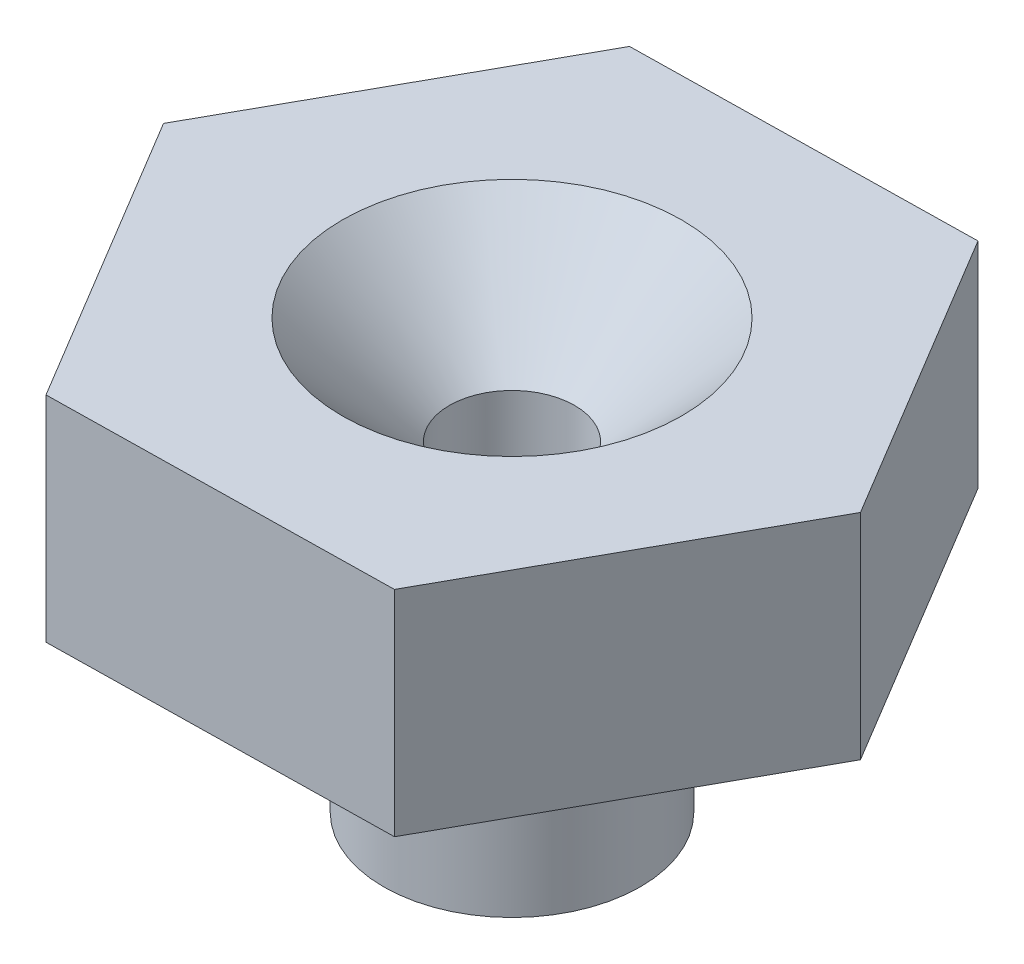
SolidWorks part; units mm, degrees
ref_plane "Front Plane" through (0, 0, 0) normal (0, 0, 1) x (1, 0, 0)
ref_plane "Top Plane" through (0, 0, 0) normal (0, 1, 0) x (1, 0, 0)
ref_plane "Right Plane" through (0, 0, 0) normal (1, 0, 0) x (0, 0, -1)
sketch "Sketch1" plane through (0, 0, 0) normal (0, 1, 0) x (1, 0, 0)
  line L1 (-15.9977, -0.2701) -> (-7.7649, -13.9895)
  line L2 (-7.7649, -13.9895) -> (8.2328, -13.7194)
  line L3 (8.2328, -13.7194) -> (15.9977, 0.2701)
  line L4 (15.9977, 0.2701) -> (7.7649, 13.9895)
  line L5 (7.7649, 13.9895) -> (-8.2328, 13.7194)
  line L6 (-8.2328, 13.7194) -> (-15.9977, -0.2701)
  circle A0 centre (0, 0) radius 16
  circle A1 centre (0, 0) radius 13.8564 construction
  dimension "D1" = 32
extrude "Boss-Extrude1" add sketch "Sketch1" along normal blind 10 contours L5 L6 L1 L2 L3 L4
sketch "Sketch2" plane through (0, 0, 0) normal (0, -1, 0) x (1, 0, 0)
  circle A0 centre (0, 0) radius 6
  dimension "D1" = 12
extrude "Boss-Extrude2" add sketch "Sketch2" along normal blind 10
sketch "Sketch3" plane through (0, -10, 0) normal (0, -1, 0) x (1, 0, 0)
  circle A0 centre (0, 0) radius 2.925
  dimension "D1" = 5.85
extrude "Cut-Extrude1" cut sketch "Sketch3" against normal through all
fillet "Fillet1" radius 4 1 edges at (0, 0, -6)
chamfer "Chamfer1" distance 5 angle 45 1 edges at (0, 10, -2.925)
